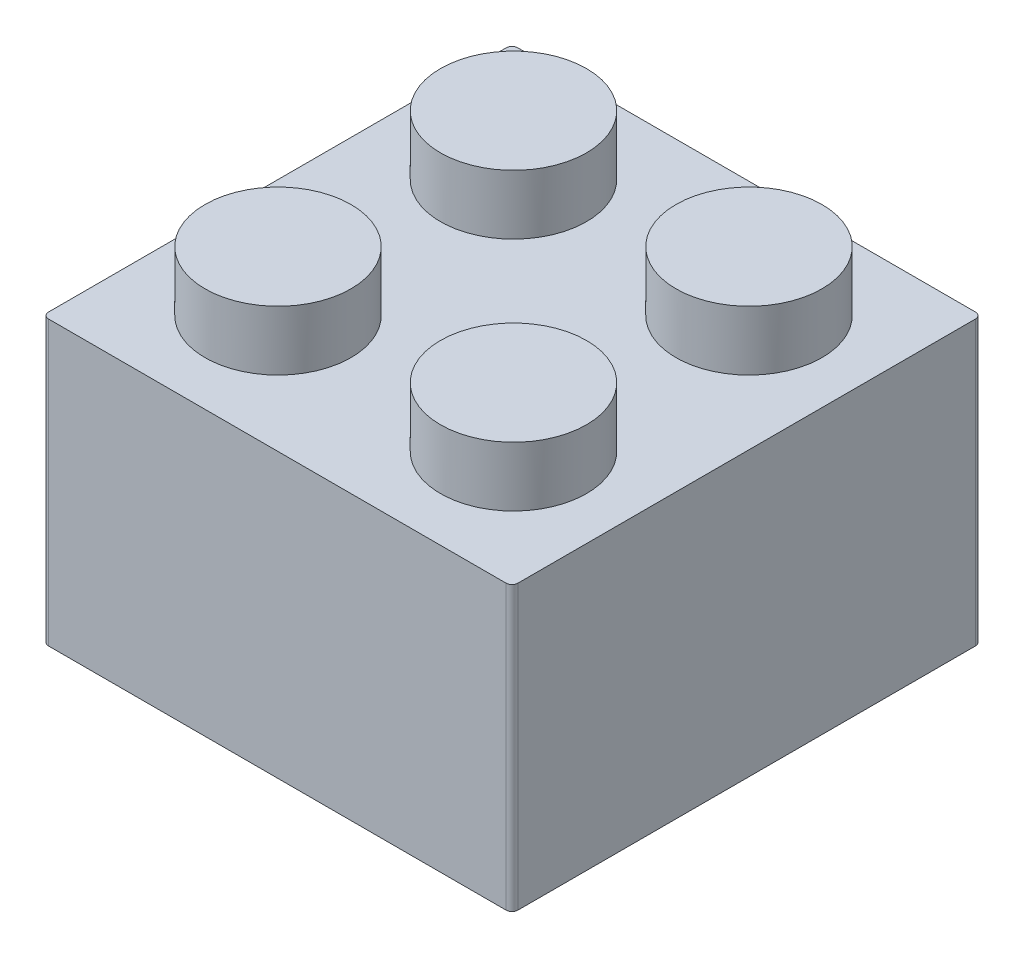
SolidWorks part; units mm, degrees
ref_plane "Front Plane" through (0, 0, 0) normal (0, 0, 1) x (1, 0, 0)
ref_plane "Top Plane" through (0, 0, 0) normal (0, 1, 0) x (1, 0, 0)
ref_plane "Right Plane" through (0, 0, 0) normal (1, 0, 0) x (0, 0, -1)
sketch "stencil" plane through (0, 0, 0) normal (0, 1, 0) x (1, 0, 0)
  line L2 (0, 0) -> (0, 3.95) construction
  line L29 (0, 0) -> (3.95, 0) construction
  line L30 (3.95, 0) -> (3.95, 3.95) construction
  line L31 (7.9, 0) -> (7.9, 3.95) construction
  line L32 (11.85, 0) -> (11.85, 3.95) construction
  line L36 (3.95, 3.95) -> (3.95, 7.9) construction
  line L37 (7.9, 3.95) -> (7.9, 7.9) construction
  line L38 (11.85, 3.95) -> (11.85, 7.9) construction
  line L39 (3.95, 7.9) -> (3.95, 11.85) construction
  line L40 (7.9, 7.9) -> (7.9, 11.85) construction
  line L41 (11.85, 7.9) -> (11.85, 11.85) construction
  line L52 (3.95, 11.85) -> (3.95, 15.8) construction
  line L53 (7.9, 11.85) -> (7.9, 15.8) construction
  line L55 (11.85, 11.85) -> (11.85, 15.8) construction
  line L56 (0, 3.95) -> (0, 7.9) construction
  line L57 (0, 7.9) -> (0, 11.85) construction
  line L58 (0, 11.85) -> (0, 15.8) construction
  line L59 (3.95, 0) -> (7.9, 0) construction
  line L60 (7.9, 0) -> (11.85, 0) construction
  line L61 (11.85, 0) -> (15.8, 0) construction
  line L62 (3.95, 3.95) -> (7.9, 3.95) construction
  line L63 (7.9, 3.95) -> (11.85, 3.95) construction
  line L64 (11.85, 3.95) -> (15.8, 3.95) construction
  line L65 (3.95, 7.9) -> (7.9, 7.9) construction
  line L66 (7.9, 7.9) -> (11.85, 7.9) construction
  line L67 (11.85, 7.9) -> (15.8, 7.9) construction
  line L68 (3.95, 11.85) -> (7.9, 11.85) construction
  line L69 (7.9, 11.85) -> (11.85, 11.85) construction
  line L70 (11.85, 11.85) -> (15.8, 11.85) construction
  line L71 (0, 3.95) -> (3.95, 3.95) construction
  line L72 (0, 7.9) -> (3.95, 7.9) construction
  line L73 (0, 11.85) -> (3.95, 11.85) construction
  line L74 (14.35, 14.35) -> (1.45, 14.35)
  line L75 (15.75, 15.75) -> (0.05, 15.75)
  line L76 (15.75, 15.75) -> (15.75, 0.05)
  line L77 (15.75, 0.05) -> (0.05, 0.05)
  line L78 (0.05, 15.75) -> (0.05, 0.05)
  line L79 (7.9, 0.05) -> (7.9, 15.75) construction
  line L80 (15.75, 7.9) -> (0.05, 7.9) construction
  line L81 (1.45, 14.35) -> (1.45, 1.45)
  line L82 (14.35, 1.45) -> (1.45, 1.45)
  line L83 (14.35, 14.35) -> (14.35, 1.45)
  circle A40 centre (7.9, 7.9) radius 3.25
  circle A41 centre (7.9, 7.9) radius 2.45
  circle A42 centre (3.95, 3.95) radius 2.45
  circle A43 centre (11.85, 3.95) radius 2.45
  circle A44 centre (11.85, 11.85) radius 2.45
  circle A45 centre (3.95, 11.85) radius 2.45
  point P6 (3.95, -15.8)
  point P9 (7.9, -15.8)
  point P10 (7.9, -11.85)
  point P13 (3.95, -7.9)
  point P15 (7.9, -7.9)
  point P17 (7.9, -3.95)
  point P18 (3.95, 0)
  point P21 (7.9, 0)
  point P25 (7.9, 3.95)
  point P27 (3.95, 7.9)
  point P28 (7.9, 7.9)
  point P29 (0, -11.85)
  point P30 (0, -7.9)
  point P31 (0, 3.95)
  point P34 (0, -3.95)
  point P36 (0, 15.8)
  point P37 (0, 23.7)
  point P38 (7.9, 23.7)
  point P39 (15.8, 23.7)
  point P40 (15.8, 15.8)
  point P41 (15.8, 7.9)
  dimension "D9" = 6.5
  dimension "D11" = 4.9
  dimension "D1" = 3.95
  dimension "D2" = 3.95
  dimension "D3" = 15.7
  dimension "D8" = 15.7
  dimension "D10" = 0.8
  dimension "D12" = 1.4
  dimension "D4" = 4
  dimension "D5" = 4
  dimension "D6" = 4
  dimension "D7" = 4
sketch "Sketch1" plane through (0, 0, 0) normal (0, 1, 0) x (1, 0, 0)
  line L5 (0, 0) -> (15.75, 0)
  line L6 (0, 0) -> (0, 15.75)
  line L7 (0, 15.75) -> (15.75, 15.75)
  line L8 (15.75, 0) -> (15.75, 15.75)
extrude "Boss-Extrude1" add sketch "Sketch1" along normal mid plane 9.5
sketch "Sketch2" plane through (0, 4.75, 0) normal (0, 1, 0) x (1, 0, 0)
  circle A9 centre (3.95, 3.95) radius 2.45
  circle A10 centre (3.95, 3.95) radius 2.45 construction
  circle A11 centre (11.85, 3.95) radius 2.45
  circle A12 centre (11.85, 11.85) radius 2.45
  circle A13 centre (3.95, 11.85) radius 2.45
extrude "Boss-Extrude2" add sketch "Sketch2" along normal blind 2
sketch "Sketch4" plane through (0, -4.75, 0) normal (0, -1, 0) x (1, 0, 0)
  line L6 (1.45, -1.45) -> (14.35, -1.45)
  line L8 (1.45, -1.45) -> (1.45, -14.35)
  line L9 (1.45, -14.35) -> (14.35, -14.35)
  line L10 (14.35, -1.45) -> (14.35, -14.35)
extrude "Cut-Extrude1" cut sketch "Sketch4" against normal blind 4
sketch "Sketch5" plane through (0, -0.75, 0) normal (0, -1, 0) x (1, 0, 0)
  circle A8 centre (7.9, -7.9) radius 3.25
  circle A9 centre (7.9, -7.9) radius 2.45
  circle A10 centre (7.9, -7.9) radius 3.25 construction
  circle A11 centre (7.9, -7.9) radius 2.45 construction
extrude "Boss-Extrude3" add sketch "Sketch5" along normal up to surface (4 mm away) up to face at (7.9, -4.75, -7.9)
sketch "Sketch7" plane through (0, -0.75, 0) normal (0, -1, 0) x (1, 0, 0)
  line L0 (3.95, -11.85) -> (3.95, -15.8) construction
  line L1 (0, -11.85) -> (3.95, -11.85) construction
  line L2 (0, -3.95) -> (3.95, -3.95) construction
  line L3 (3.95, 0) -> (3.95, -3.95) construction
  line L4 (11.85, 0) -> (11.85, -3.95) construction
  line L5 (11.85, -3.95) -> (15.8, -3.95) construction
  line L6 (11.85, -11.85) -> (15.8, -11.85) construction
  line L7 (11.85, -11.85) -> (11.85, -15.8) construction
  line L8 (14.35, -14.35) -> (1.45, -14.35) construction
  line L9 (1.45, -14.35) -> (1.45, -1.45) construction
  line L10 (14.35, -1.45) -> (1.45, -1.45) construction
  line L11 (14.35, -14.35) -> (14.35, -1.45) construction
  circle A0 centre (3.95, -14.35) radius 0.25
  circle A1 centre (1.45, -11.85) radius 0.25
  circle A2 centre (1.45, -3.95) radius 0.25
  circle A3 centre (3.95, -1.45) radius 0.25
  circle A4 centre (11.85, -1.45) radius 0.25
  circle A5 centre (14.35, -3.95) radius 0.25
  circle A6 centre (14.35, -11.85) radius 0.25
  circle A7 centre (11.85, -14.35) radius 0.25
  dimension "D1" = 0.5
extrude "Boss-Extrude4" [suppressed] add sketch "Sketch7" along normal up to surface (4 mm away)
fillet "Fillet1" radius 0.2 4 edges at (0, 0, -15.75) (15.75, 0, -15.75) (15.75, 0, 0) (0, 0, 0)
equation "\"t\"= 0.1'tolerance"
equation "\"D3@stencil\"=15.8-\"t\""
equation "\"D8@stencil\"=15.8-\"t\""
equation "\"D12@stencil\"=1.50-\"t\""
